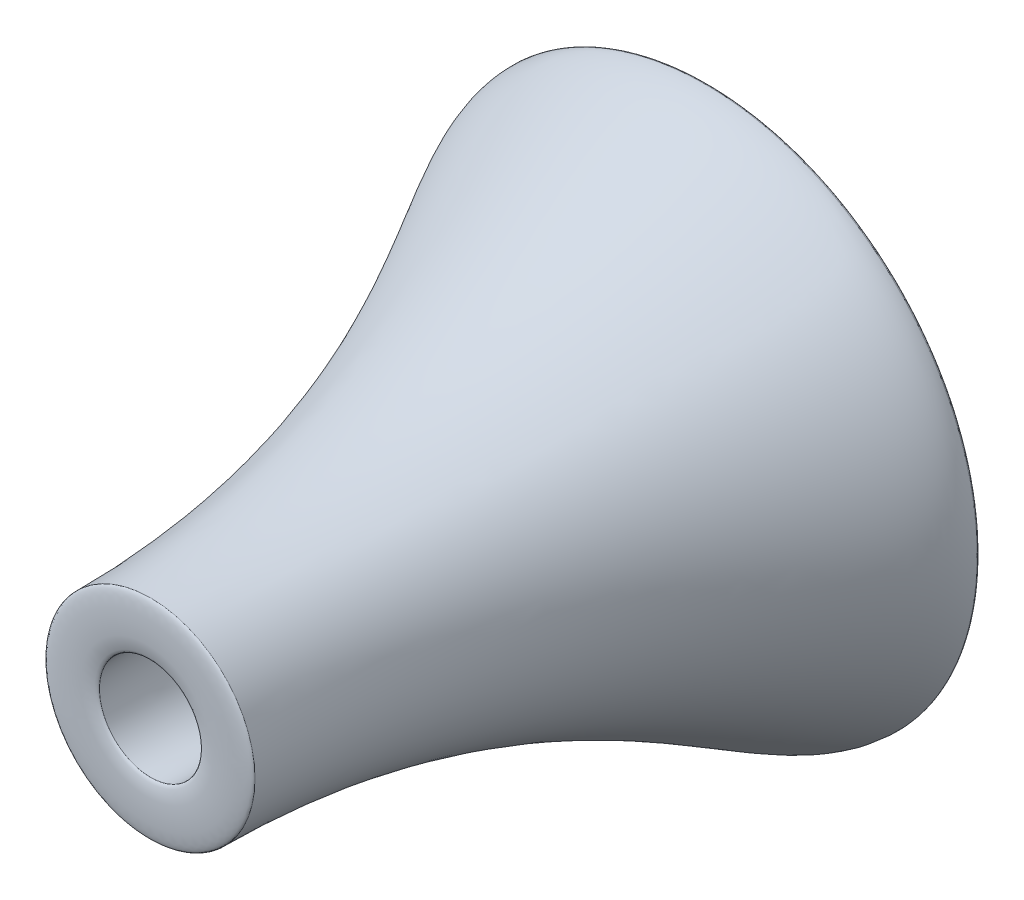
SolidWorks part; units mm, degrees
ref_plane "Front Plane" through (0, 0, 0) normal (0, 0, 1) x (1, 0, 0)
ref_plane "Top Plane" through (0, 0, 0) normal (0, 1, 0) x (1, 0, 0)
ref_plane "Right Plane" through (0, 0, 0) normal (1, 0, 0) x (0, 0, -1)
sketch "Sketch1" plane through (0, 0, 0) normal (0, 0, 1) x (1, 0, 0)
  circle A0 centre (0, 0) radius 50.8
  dimension "D1" = 101.6
ref_plane "Plane1" through (0, -254, 0) normal (0, 1, 0) x (1, 0, 0)
sketch "Sketch6" plane through (0, 0, 0) normal (0, 1, 0) x (1, 0, 0)
  line L0 (0, -99.6848) -> (0, 145.6048) construction
ref_plane "Plane2" through (0, -114.3, 0) normal (0, 1, 0) x (1, 0, 0)
sketch "Sketch12" plane through (0, 0, 0) normal (0, 1, 0) x (1, 0, 0)
  line L0 (0, -1104.7568) -> (0, -908.6135) construction
ref_plane "Plane3" through (0, 0, 203.2) normal (0, 0, 1) x (1, 0, 0)
ref_plane "Plane4" through (0, 0, 889) normal (0, 0, 1) x (1, 0, 0)
sketch "Sketch17" plane through (0, 0, 0) normal (0, 1, 0) x (1, 0, 0)
  line L0 (-259.4955, -43.5301) -> (-259.4955, 70.1436) construction
  line L1 (-110.6437, -1316.1124) -> (-110.6437, -853.5386) construction
  line L2 (-259.4955, 45.4622) -> (-387.328, 45.4622)
  line L3 (-387.328, 45.4622) -> (-387.328, -1084.8928)
  line L4 (-387.328, -1084.8928) -> (-110.6437, -1084.8928)
  spline S0 degree 3 poles (-259.4955, 45.4622) (-259.4955, -7.1736) (-207.7477, -105.8122) (-173.3147, -383.1384) (-92.4228, -818.9689) (-110.6437, -795.7842) (-110.6437, -1084.8928) knots 0 0 0 0 0.158009 0.206507 0.484977 1 1 1 1
sketch "Sketch21" plane through (0, 0, 0) normal (0, 1, 0) x (1, 0, 0)
  line L0 (-587.8935, -22.8536) -> (-587.8935, 113.778) construction
  line L1 (-225.524, -1315.9117) -> (-225.524, -853.874) construction
  line L2 (-485.6867, 117.9157) -> (-587.8935, 117.9157) construction
  line L3 (-110.6437, -1080.6912) -> (-225.524, -1080.6912) construction
  line L4 (-110.6437, -1080.6912) -> (-225.524, -1080.6912)
  line L6 (-485.6867, 117.9157) -> (-587.8935, 117.9157)
  spline S0 degree 3 poles (-485.6867, 117.9157) (-485.6867, 65.2799) (-363.7411, -68.8838) (-348.5636, -337.828) (-153.2079, -723.8743) (-110.6437, -791.5826) (-110.6437, -1080.6912) knots 0 0 0 0 0.158009 0.206507 0.484977 1 1 1 1
  spline S1 degree 3 poles (-587.8935, 117.9157) (-587.8935, -7.4683) (-225.524, -350.3821) (-225.524, -1080.6912) knots 0 0 0 0 1 1 1 1
  point P10 (0, 0)
  point P11 (-225.524, -1080.6912)
  point P12 (-587.8935, 71.4581)
  point P13 (-485.6867, 117.9157)
  point P14 (-360.2511, -158.5072)
  point P15 (-225.524, -578.9488)
revolve "Revolve2" add sketch "Sketch21" angle 360 about L0
sketch "Sketch22" plane through (0, 0, 0) normal (0, 1, 0) x (1, 0, 0)
  line L0 (-587.8935, 117.9157) -> (-485.6867, 117.9157)
  line L1 (-485.6867, 114.1066) -> (-485.6867, 121.7248) construction
  line L2 (-587.8935, 119.3084) -> (-587.8935, 116.5229) construction
  spline S0 degree 3 poles (-587.8935, 117.9157) (-587.8935, 134.849) (-485.6867, 134.849) (-485.6867, 117.9157) knots 0 0 0 0 1 1 1 1
revolve "Revolve3" add sketch "Sketch22" angle 360 about L0
sketch "Sketch23" plane through (0, 0, 0) normal (0, 1, 0) x (1, 0, 0)
  line L0 (-225.524, -1080.6912) -> (-110.6437, -1080.6912)
  line L1 (-225.524, -1089.9023) -> (-225.524, -1071.4802) construction
  line L2 (-110.6437, -1070.1182) -> (-110.6437, -1091.2642) construction
  spline S0 degree 3 poles (-225.524, -1080.6912) (-225.524, -1093.3912) (-110.6437, -1093.3912) (-110.6437, -1080.6912) knots 0 0 0 0 1 1 1 1
revolve "Revolve4" add sketch "Sketch23" angle 360 about L0
ref_plane "Plane5" through (289.9098, 0, 0) normal (1, 0, 0) x (0, 0, -1)
sketch "Sketch24" plane through (289.9098, 0, 0) normal (1, 0, 0) x (0, 0, -1)
  line L0 (-1123.5724, -17.6357) -> (119.2276, -17.6357) construction
  line L1 (-1080.6912, 0) -> (117.9157, 0) construction
  line L2 (-1080.6912, -225.524) -> (-1080.6912, 225.524) construction
  line L3 (117.9157, 587.8935) -> (117.9157, -587.8935) construction
  text T0 "MD-130 Gas Turbine Engine" font "TI-Nspire" height in points 160
